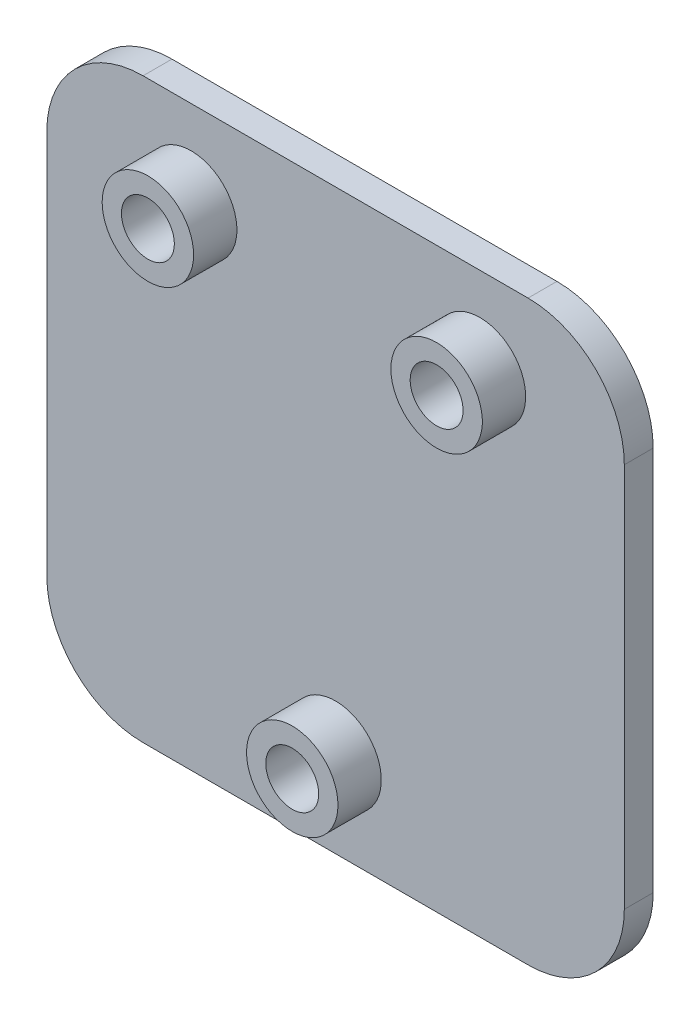
SolidWorks part; units mm, degrees
ref_plane "Front Plane" through (0, 0, 0) normal (0, 0, 1) x (1, 0, 0)
ref_plane "Top Plane" through (0, 0, 0) normal (0, 1, 0) x (1, 0, 0)
ref_plane "Right Plane" through (0, 0, 0) normal (1, 0, 0) x (0, 0, -1)
sketch "Sketch1" plane through (0, 0, 0) normal (0, 0, 1) x (1, 0, 0)
  line L4 (-30, 0) -> (30, 0) construction
  line L9 (-20, -30) -> (20, -30)
  line L10 (-30, -20) -> (-30, 20)
  line L11 (-20, 30) -> (20, 30)
  line L12 (30, -20) -> (30, 20)
  line L13 (-30, -30) -> (30, 30) construction
  line L14 (-30, 30) -> (30, -30) construction
  line L15 (-15, 21) -> (-15, -21) construction
  line L16 (0, 30) -> (0, 0) construction
  line L17 (-15, -21) -> (0, -21) construction
  circle A0 centre (-15, 21) radius 2.75
  circle A1 centre (0, -21) radius 2.75
  circle A2 centre (15, 21) radius 2.75
  arc A3 (-30, 20) -> (-20, 30) centre (-20, 20) cw
  arc A4 (-20, -30) -> (-30, -20) centre (-20, -20) cw
  arc A5 (20, -30) -> (30, -20) centre (20, -20) ccw
  arc A6 (20, 30) -> (30, 20) centre (20, 20) cw
  point P0 (0, 0)
  point P6 (34.69, 30.1775)
  point P15 (-15, 0)
  dimension "D1" = 5.5
  dimension "D3" = 15
  dimension "D6" = 10
  dimension "D2" = 42
  dimension "D4" = 60
  dimension "D5" = 60
extrude "Boss-Extrude1" add sketch "Sketch1" along normal blind 3
sketch "Sketch6" plane through (0, 0, 3) normal (0, 0, 1) x (1, 0, 0)
  line L0 (0, 0) -> (0, 30) construction
  line L1 (20, 30) -> (-20, 30) construction
  circle A0 centre (-15, 21) radius 4.75
  circle A1 centre (0, -21) radius 4.75
  circle A2 centre (-15, 21) radius 2.75
  circle A3 centre (0, -21) radius 2.75
  circle A4 centre (0, -21) radius 2.75 construction
  circle A5 centre (-15, 21) radius 2.75 construction
  circle A6 centre (15, 21) radius 2.75
  circle A7 centre (15, 21) radius 4.75
  dimension "D1" = 2
extrude "Boss-Extrude3" add sketch "Sketch6" along normal blind 4.5
